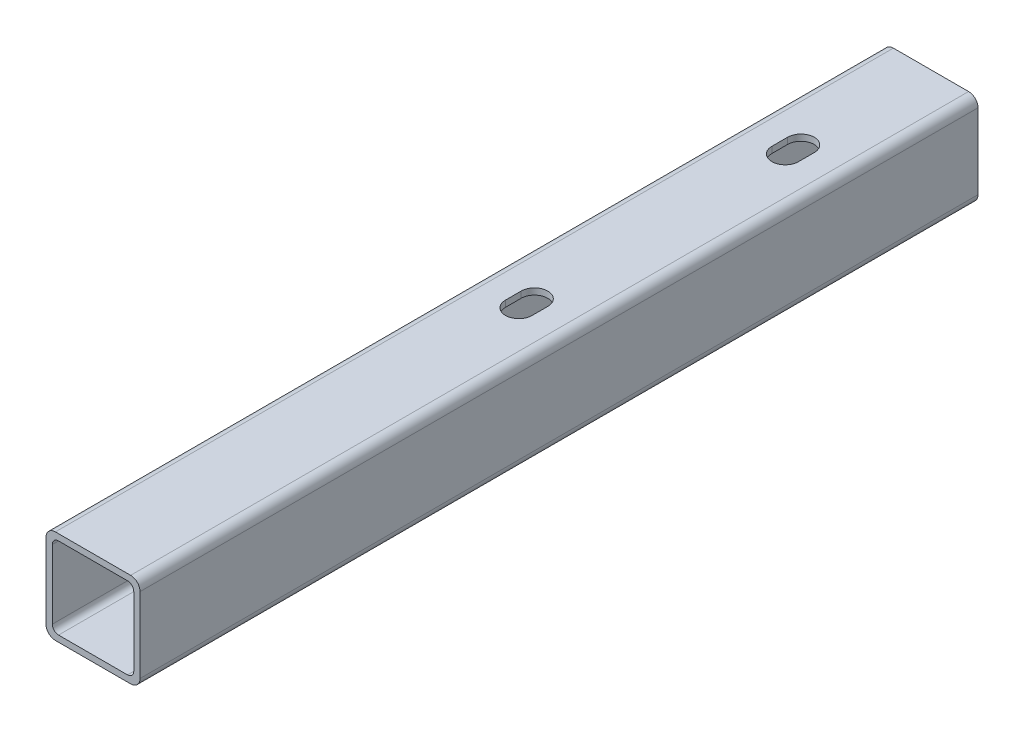
SolidWorks part; units mm, degrees
material "AISI 1020"
ref_plane "Спереди" through (0, 0, 0) normal (0, 0, 1) x (1, 0, 0)
ref_plane "Сверху" through (0, 0, 0) normal (0, 1, 0) x (1, 0, 0)
ref_plane "Справа" through (0, 0, 0) normal (1, 0, 0) x (0, 0, -1)
sketch "Эскиз1" plane through (0, 0, 0) normal (0, 0, 1) x (1, 0, 0)
  line L1 (37, 0) -> (-137, 0) construction
  line L2 (0, 0) -> (30, 0) construction
  line B0 (3, 0) -> (27, 0)
  line B1 (0, -3) -> (0, -27)
  line B2 (3, -30) -> (27, -30)
  line B3 (30, -3) -> (30, -27)
  line B4 (4, -2) -> (26, -2)
  line B5 (2, -4) -> (2, -26)
  line B6 (4, -28) -> (26, -28)
  line B7 (28, -4) -> (28, -26)
  arc B8 (0, -27) -> (3, -30) centre (3, -27) ccw
  arc B9 (27, -30) -> (30, -27) centre (27, -27) ccw
  arc B10 (27, 0) -> (30, -3) centre (27, -3) cw
  arc B11 (3, 0) -> (0, -3) centre (3, -3) ccw
  arc B12 (2, -26) -> (4, -28) centre (4, -26) ccw
  arc B13 (26, -28) -> (28, -26) centre (26, -26) ccw
  arc B14 (26, -2) -> (28, -4) centre (26, -4) cw
  arc B15 (4, -2) -> (2, -4) centre (4, -4) ccw
sketch_block_instance "Блок-30х30х2-1"
sketch_block "Блок-30х30х2" parameters "D3"=3, "D4"=2, "D1"=30, "D2"=2
extrude "Бобышка-Вытянуть1" add sketch "Эскиз1" against normal offset from surface (267.3363 mm away) 35
sketch "Эскиз2" plane through (0, -30, 0) normal (0, -1, 0) x (1, 0, 0)
  line L0 (15, -138.3363) -> (15, -223.3363) construction
  line L1 (15, -135.8363) -> (15, -140.8363) construction
  line L2 (19.25, -135.8363) -> (19.25, -140.8363)
  line L3 (10.75, -135.8363) -> (10.75, -140.8363)
  line L4 (15, -225.8363) -> (15, -220.8363) construction
  line L5 (10.75, -225.8363) -> (10.75, -220.8363)
  line L6 (19.25, -225.8363) -> (19.25, -220.8363)
  arc A0 (19.25, -135.8363) -> (10.75, -135.8363) centre (15, -135.8363) ccw
  arc A1 (10.75, -140.8363) -> (19.25, -140.8363) centre (15, -140.8363) ccw
  circle A2 centre (15, -138.3363) radius 4.25 construction
  arc A3 (10.75, -225.8363) -> (19.25, -225.8363) centre (15, -225.8363) ccw
  arc A4 (19.25, -220.8363) -> (10.75, -220.8363) centre (15, -220.8363) ccw
  point P6 (15, -138.3363)
  point P15 (15, -223.3363)
  dimension "D1" = 2.5
extrude "Вырез-Вытянуть1" cut sketch "Эскиз2" against normal through all
sketch "Эскиз3" plane through (0, -30, 0) normal (0, -1, 0) x (1, 0, 0)
  line L0 (15, -140.8363) -> (15, -135.8363) construction
  line L1 (5, -140.8363) -> (5, -135.8363)
  line L2 (25, -140.8363) -> (25, -135.8363)
  line L3 (15, -225.8363) -> (15, -220.8363) construction
  line L4 (5, -225.8363) -> (5, -220.8363)
  line L5 (25, -225.8363) -> (25, -220.8363)
  arc A0 (5, -140.8363) -> (25, -140.8363) centre (15, -140.8363) ccw
  arc A1 (25, -135.8363) -> (5, -135.8363) centre (15, -135.8363) ccw
  arc A2 (5, -225.8363) -> (25, -225.8363) centre (15, -225.8363) ccw
  arc A3 (25, -220.8363) -> (5, -220.8363) centre (15, -220.8363) ccw
  point P2 (15, -138.3363)
  point P11 (15, -223.3363)
  dimension "D1" = 20
extrude "Вырез-Вытянуть2" cut sketch "Эскиз3" against normal blind 10
